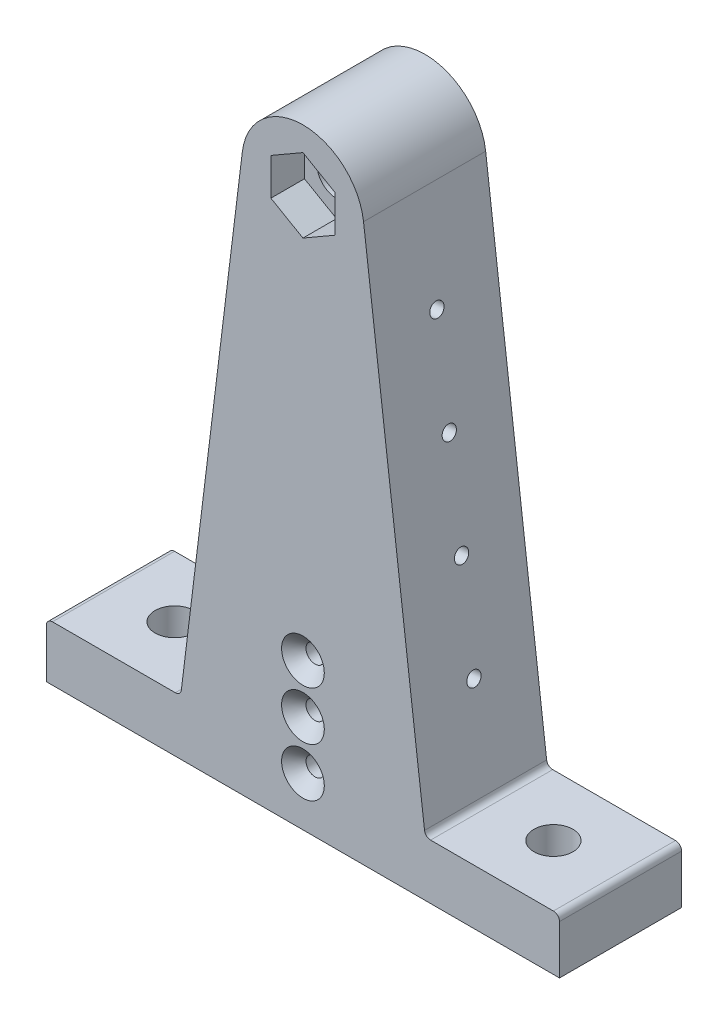
SolidWorks part; units mm, degrees
ref_plane "Front Plane" through (0, 0, 0) normal (0, 0, 1) x (1, 0, 0)
ref_plane "Top Plane" through (0, 0, 0) normal (0, 1, 0) x (1, 0, 0)
ref_plane "Right Plane" through (0, 0, 0) normal (1, 0, 0) x (0, 0, -1)
sketch "Sketch1" plane through (0, 0, 0) normal (0, 0, 1) x (1, 0, 0)
  line L0 (-9.9255, 1.2187) -> (-20.0206, -81)
  line L1 (-20.0206, -81) -> (-42.0206, -81)
  line L2 (-42.0206, -81) -> (-42.0206, -90)
  line L3 (-42.0206, -90) -> (42.0206, -90)
  line L4 (0, 0) -> (0, -90) construction
  line L5 (42.0206, -81) -> (42.0206, -90)
  line L6 (20.0206, -81) -> (42.0206, -81)
  line L7 (9.9255, 1.2187) -> (20.0206, -81)
  circle A0 centre (0, 0) radius 3.2
  circle A1 centre (0, 0) radius 10
  dimension "D1" = 6.4
  dimension "D2" = 20
  dimension "D3" = 90
  dimension "D4" = 9
  dimension "D5" = 22
  dimension "D6" = 7
extrude "Boss-Extrude1" add sketch "Sketch1" along normal blind 20
sketch "Sketch3" plane through (0, -81, 0) normal (0, 1, 0) x (1, 0, 0)
  line L0 (-42.0206, -10) -> (-31.0206, -10) construction
  line L1 (-42.0206, -20) -> (-42.0206, 0) construction
  line L2 (42.0206, -10) -> (31.0206, -10) construction
  line L3 (42.0206, -20) -> (42.0206, 0) construction
  circle A0 centre (-31.0206, -10) radius 3.2
  circle A1 centre (31.0206, -10) radius 3.2
  circle A2 centre (-31.0206, -10) radius 9.5
  circle A3 centre (31.0206, -10) radius 9.5
  dimension "D1" = 6.4
  dimension "D2" = 19
  dimension "D3" = 11
extrude "Cut-Extrude1" cut sketch "Sketch3" against normal through all contours A0 | A1
sketch "Sketch4" plane through (0, 0, 20) normal (0, 0, 1) x (1, 0, 0)
  line L1 (0, 6.0622) -> (-5.25, 3.0311)
  line L2 (-5.25, 3.0311) -> (-5.25, -3.0311)
  line L3 (-5.25, -3.0311) -> (0, -6.0622)
  line L4 (0, -6.0622) -> (5.25, -3.0311)
  line L5 (5.25, -3.0311) -> (5.25, 3.0311)
  line L6 (5.25, 3.0311) -> (0, 6.0622)
  circle A0 centre (0, 0) radius 5.25 construction
  dimension "D1" = 10.5
extrude "Cut-Extrude2" cut sketch "Sketch4" against normal blind 5.5
sketch "Sketch6" plane through (0, 0, 20) normal (0, 0, 1) x (1, 0, 0)
  line L0 (0, -90) -> (0, -82) construction
  line L1 (-42.0206, -90) -> (42.0206, -90) construction
  line L2 (0, -82) -> (0, -74) construction
  line L3 (0, -74) -> (0, -66) construction
  circle A0 centre (0, -66) radius 1.5
  circle A1 centre (0, -74) radius 1.5
  circle A2 centre (0, -82) radius 1.5
  dimension "D1" = 3
  dimension "D2" = 8
extrude "Cut-Extrude4" cut sketch "Sketch6" against normal through all
chamfer "Chamfer1" distance 2 angle 45 3 edges at (1.5, -82, 20) (1.5, -74, 20) (1.5, -66, 20)
sketch "Sketch8" plane through (-9.9255, 1.2187, 0) normal (-0.9925, 0.1219, 0) x (0, 0, 1)
  line L0 (10, 0) -> (10, -16.5672) construction
  line L3 (20, 0) -> (0, 0) construction
  line L4 (10, -16.5672) -> (10, -33.1345) construction
  line L5 (10, -33.1345) -> (10, -49.7017) construction
  line L6 (10, -49.7017) -> (10, -66.2689) construction
  line L7 (10, -66.2689) -> (10, -82.8361) construction
  line L8 (20, -82.8361) -> (0, -82.8361) construction
  circle A0 centre (10, -16.5672) radius 1.16
  circle A1 centre (10, -33.1345) radius 1.16
  circle A2 centre (10, -49.7017) radius 1.16
  circle A3 centre (10, -66.2689) radius 1.16
  dimension "D1" = 2.32
extrude "Cut-Extrude5" cut sketch "Sketch8" against normal blind 10
mirror "Mirror1" about plane through (0, 0, 0) normal (1, 0, 0) of "Cut-Extrude5"
fillet "Fillet1" radius 1 4 edges at (-42.0206, -81, 10) (-20.0206, -81, 10) (42.0206, -81, 10) (20.0206, -81, 10)
